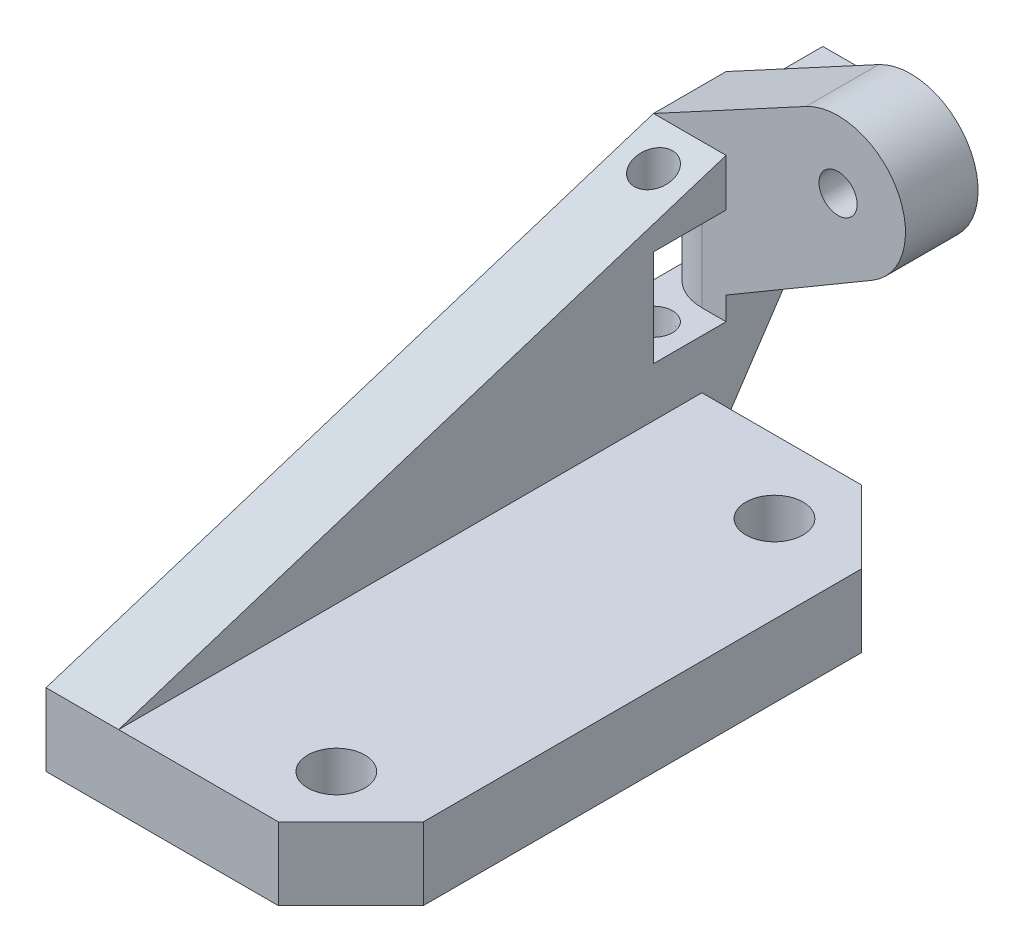
SolidWorks part; units mm, degrees
ref_plane "Front Plane" through (0, 0, 0) normal (0, 0, 1) x (1, 0, 0)
ref_plane "Top Plane" through (0, 0, 0) normal (0, 1, 0) x (1, 0, 0)
ref_plane "Right Plane" through (0, 0, 0) normal (1, 0, 0) x (0, 0, -1)
sketch "Sketch1" plane through (0, 0, 0) normal (0, 1, 0) x (1, 0, 0)
  line L0 (7.62, 30.62) -> (7.62, 26.81) construction
  line L1 (0, 0) -> (12.192, 0)
  line L2 (0, 0) -> (0, 30.62)
  line L3 (0, 30.62) -> (12.192, 30.62)
  line L4 (12.192, 0) -> (12.192, 30.62)
  line L5 (7.62, 26.81) -> (7.62, 3.81) construction
  line L6 (7.62, 3.81) -> (7.62, 0) construction
  circle A0 centre (7.62, 26.81) radius 1.5
  circle A1 centre (7.62, 3.81) radius 1.5
  dimension "D1" = 3
  dimension "D2" = 23
  dimension "D3" = 4.572
  dimension "D4" = 3.81
  dimension "D5" = 7.62
extrude "Boss-Extrude1" add sketch "Sketch1" along normal blind 3.81
sketch "Sketch2" plane through (0, 0, 0) normal (-1, 0, 0) x (0, 0, 1)
  line L0 (0, 3.81) -> (0, 0) construction
  line L1 (-30.62, 0) -> (0, 0) construction
  line L2 (0, 3.81) -> (0, 0)
  line L3 (-30.62, 0) -> (0, 0)
  line L4 (-30.62, 0) -> (-35.7, 7.62)
  line L5 (-35.7, 7.62) -> (-35.7, 13.97)
  line L7 (-30.62, 3.81) -> (-30.62, 0) construction
  line L8 (-35.7, 13.97) -> (-31.89, 13.97)
  line L9 (-31.89, 13.97) -> (0, 3.81)
  dimension "D1" = 5.08
  dimension "D2" = 7.62
  dimension "D3" = 6.35
  dimension "D4" = 3.81
extrude "Boss-Extrude2" add sketch "Sketch2" along normal blind 3.81
sketch "Sketch3" plane through (0, 0, -35.7) normal (0, 0, -1) x (-1, 0, 0)
  line L0 (3.81, 13.97) -> (3.81, 7.62) construction
  line L1 (3.81, 7.62) -> (2.032, 7.62)
  line L2 (3.81, 7.62) -> (3.81, 9.398)
  line L3 (3.81, 9.398) -> (2.032, 9.398)
  line L4 (2.032, 7.62) -> (2.032, 9.398)
  line L5 (3.81, 10.795) -> (2.032, 10.795)
  line L6 (3.81, 10.795) -> (3.81, 12.573)
  line L7 (3.81, 12.573) -> (2.032, 12.573)
  line L8 (2.032, 10.795) -> (2.032, 12.573)
  dimension "D1" = 1.778
  dimension "D2" = 1.778
extrude "Boss-Extrude3" add sketch "Sketch3" along normal blind 5.08
sketch "Sketch4" plane through (0, 0, -35.7) normal (0, 0, -1) x (-1, 0, 0)
  line L0 (0, 7.62) -> (-7.6703, 12.1238)
  line L1 (-4.1963, 18.2917) -> (3.81, 13.97)
  line L2 (3.81, 13.97) -> (0, 13.97)
  line L3 (0, 13.97) -> (0, 7.62)
  line L4 (-995.809, 10.0965) -> (49004.191, 10.0965) construction
  line L5 (2.032, 9.398) -> (3.81, 9.398) construction
  line L6 (2.032, 9.398) -> (2.032, 10.795) construction
  line L7 (2.032, 10.795) -> (3.81, 10.795) construction
  line L8 (3.81, 9.398) -> (3.81, 10.795) construction
  line L9 (2.032, 9.398) -> (3.81, 10.795) construction
  line L10 (2.032, 10.795) -> (3.81, 9.398) construction
  line L11 (-5.8778, 15.1765) -> (2.921, 10.0965) construction
  circle A0 centre (-5.8778, 15.1765) radius 1
  arc A1 (-7.6703, 12.1238) -> (-4.1963, 18.2917) centre (-5.8778, 15.1765) cw
  point P12 (2.921, 10.0965)
  dimension "D2" = 2.54
  dimension "D3" = 2
  dimension "D1" = 30
  dimension "D4" = 10.16
extrude "Boss-Extrude4" add sketch "Sketch4" against normal up to vertex (3.81 mm away) up to point (0, 13.97, -31.89)
sketch "Sketch5" plane through (-3.81, 0, 0) normal (-1, 0, 0) x (0, 0, 1)
  line L0 (0, 3.81) -> (-31.89, 13.97) construction
  line L1 (-31.89, 11.4862) -> (-28.08, 11.4862)
  line L2 (-31.89, 11.4862) -> (-31.89, 6.4062)
  line L3 (-31.89, 6.4062) -> (-28.08, 6.4062)
  line L4 (-28.08, 11.4862) -> (-28.08, 6.4062)
  line L5 (-28.08, 11.4862) -> (-28.08, 12.7562) construction
  line L7 (-31.89, 13.97) -> (-31.89, 18.2917) construction
  dimension "D1" = 3.81
  dimension "D2" = 5.08
  dimension "D3" = 1.27
extrude "Cut-Extrude1" cut sketch "Sketch5" against normal up to next
sketch "Sketch6" plane through (0, 6.4062, 0) normal (0, 1, 0) x (1, 0, 0)
  line L1 (0, 31.89) -> (-3.81, 31.89) construction
  line L2 (0, 31.89) -> (0, 28.08) construction
  line L3 (0, 28.08) -> (-3.81, 28.08) construction
  line L4 (-3.81, 31.89) -> (-3.81, 28.08) construction
  line L5 (0, 31.89) -> (-3.81, 28.08) construction
  line L6 (0, 28.08) -> (-3.81, 31.89) construction
  circle A0 centre (-1.905, 29.985) radius 1
  point P0 (-1.905, 29.985)
  dimension "D1" = 2
extrude "Cut-Extrude2" cut sketch "Sketch6" along normal through all and the other way blind 5.08 draft 5
chamfer "Chamfer1" distance 0.762 angle 45 3 edges at (-2.032, 10.795, -38.24) (-2.032, 9.398, -38.24) (-3.81, 9.398, -38.24)
fillet "Fillet1" radius 2.54 1 edges at (-3.81, 8.9462, -31.89)
chamfer "Chamfer2" distance 3.81 angle 45 2 edges at (12.192, 1.905, -30.62) (12.192, 1.905, 0)
fillet "Fillet2" radius 0.762 1 edges at (-3.81, 9.7155, -35.7)
